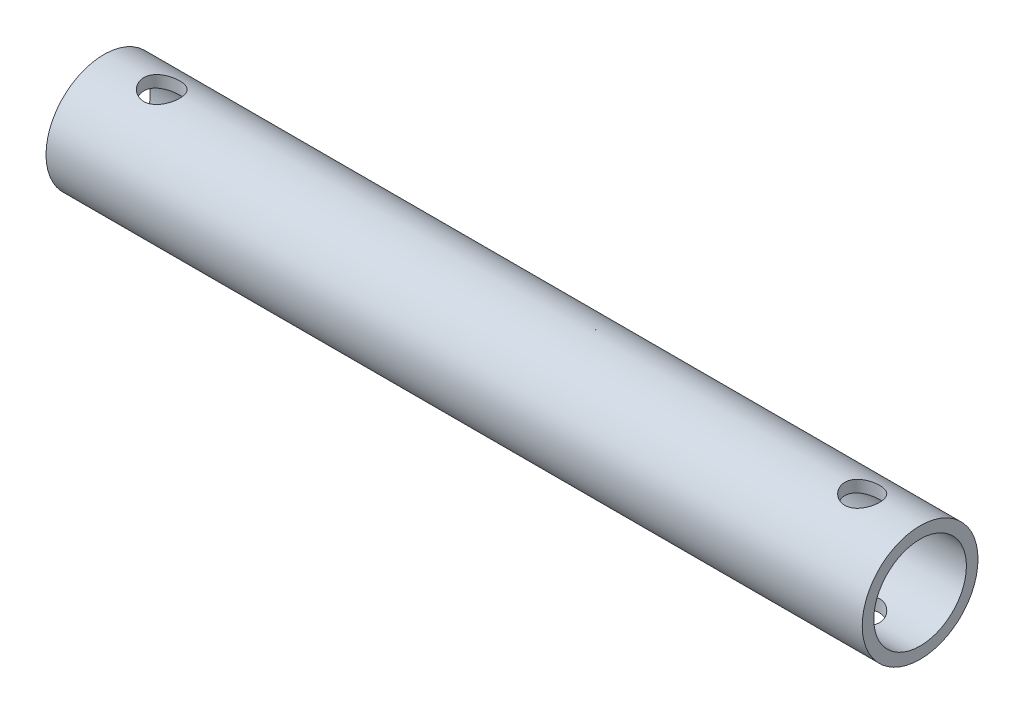
SolidWorks part; units mm, degrees
material "AISI 304"
ref_plane "前视基准面" through (0, 0, 0) normal (0, 0, 1) x (1, 0, 0)
ref_plane "上视基准面" through (0, 0, 0) normal (0, 1, 0) x (1, 0, 0)
ref_plane "右视基准面" through (0, 0, 0) normal (1, 0, 0) x (0, 0, -1)
sketch "草图1" plane through (0, 0, 0) normal (1, 0, 0) x (0, 0, -1)
  circle A0 centre (0, 0) radius 10
  circle A1 centre (0, 0) radius 8
extrude "凸台-拉伸1" add sketch "草图1" along normal blind 107
sketch "草图2" plane through (0, 0, 0) normal (-1, 0, 0) x (0, 0, 1)
  circle A0 centre (0, 0) radius 8
  circle A1 centre (0, 0) radius 10
extrude "凸台-拉伸2" add sketch "草图2" along normal blind 34
sketch "草图3" plane through (0, 0, 0) normal (0, 1, 0) x (1, 0, 0)
  line L0 (107, 0) -> (97, 0) construction
  line L1 (107, -10) -> (107, 10) construction
  circle A0 centre (97, 0) radius 3
extrude "切除-拉伸1" cut sketch "草图3" against normal mid plane 30
sketch "草图4" plane through (0, 0, 0) normal (0, 1, 0) x (1, 0, 0)
  line L0 (-34, 0) -> (-24, 0) construction
  line L1 (-34, 10) -> (-34, -10) construction
  circle A0 centre (-24, 0) radius 3.1
extrude "切除-拉伸2" cut sketch "草图4" against normal mid plane 20 contours A0
